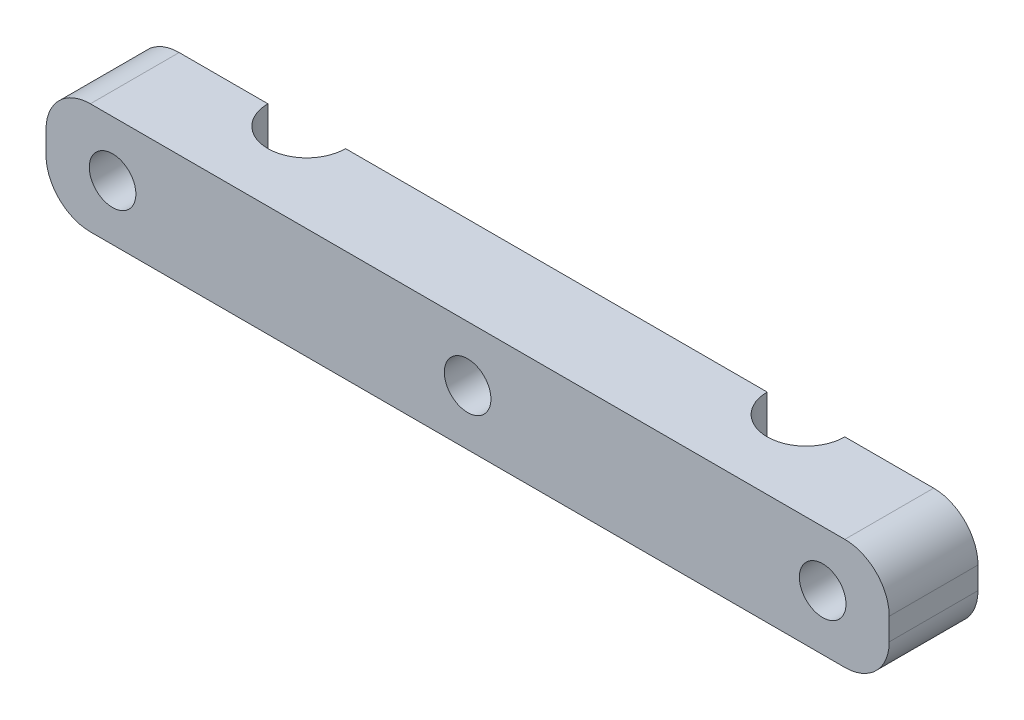
SolidWorks part; units mm, degrees
material "PE Low Density Film"
ref_plane "Front Plane" through (0, 0, 0) normal (0, 0, 1) x (1, 0, 0)
ref_plane "Top Plane" through (0, 0, 0) normal (0, 1, 0) x (1, 0, 0)
ref_plane "Right Plane" through (0, 0, 0) normal (1, 0, 0) x (0, 0, -1)
sketch "Sketch1" plane through (0, 0, 0) normal (0, 1, 0) x (1, 0, 0)
  line L0 (0, 0) -> (0, 2.5) construction
  line L1 (-38, -8) -> (38, -8)
  line L2 (-38, -8) -> (-38, 0)
  line L4 (38, -8) -> (38, 0)
  line L5 (-38, -8) -> (0, 0) construction
  line L6 (0, 0) -> (38, -8) construction
  line L7 (-19, 0) -> (19, 0) construction
  line L8 (-38, 0) -> (-26, 0)
  line L9 (-19, 0) -> (19, 0)
  line L10 (26, 0) -> (38, 0)
  arc A0 (19, 0) -> (26, 0) centre (22.5, 0) ccw
  arc A1 (-19, 0) -> (-26, 0) centre (-22.5, 0) cw
  point P0 (0, 0)
  dimension "D1" = 7
  dimension "D2" = 45
  dimension "D3" = 8
  dimension "D4" = 76
extrude "Boss-Extrude1" add sketch "Sketch1" along normal blind 10
sketch "Sketch2" plane through (0, 0, 0) normal (0, 0, -1) x (-1, 0, 0)
  line L0 (0, 0) -> (0, 5) construction
  line L1 (26, 0) -> (38, 0) construction
  circle A0 centre (32, 5) radius 2.1
  circle A1 centre (-32, 5) radius 2.1
  circle A2 centre (0, 5) radius 2.1
  dimension "D1" = 5
  dimension "D2" = 4.2
  dimension "D3" = 32
extrude "Cut-Extrude1" cut sketch "Sketch2" against normal through all
fillet "Fillet1" radius 4 4 edges at (38, 0, 4) (38, 10, 4) (-38, 0, 4) (-38, 10, 4)
